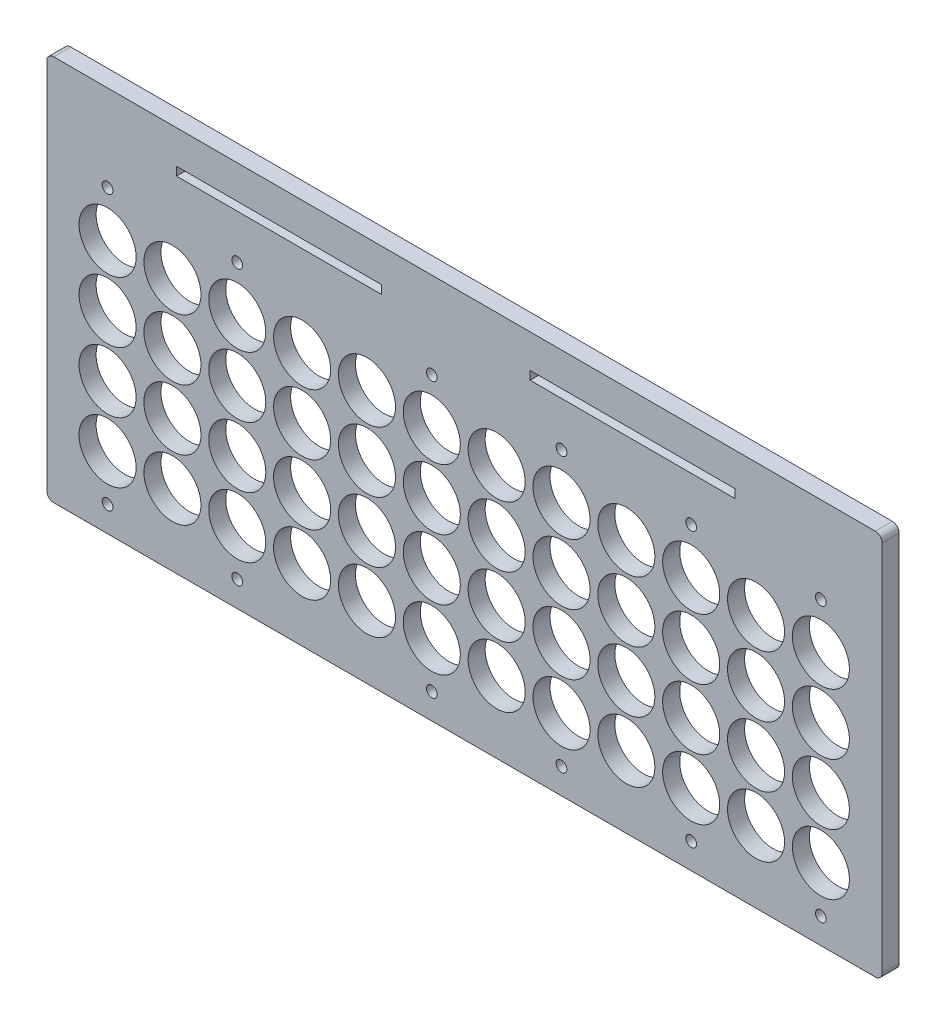
SolidWorks part; units mm, degrees
material "ABS"
ref_plane "X-Y Datum" through (0, 0, 0) normal (0, 0, 1) x (1, 0, 0)
ref_plane "X-Z Datum" through (0, 0, 0) normal (0, 1, 0) x (1, 0, 0)
ref_plane "Y-Z Datum" through (0, 0, 0) normal (1, 0, 0) x (0, 0, -1)
sketch "Sketch1" plane through (0, 0, 0) normal (0, 0, 1) x (1, 0, 0)
  line L1 (-10.2406, 8) -> (78.318, 8)
  line L2 (-10.2406, 8) -> (-10.2406, 16.1972)
  line L7 (-10.2406, 16.1972) -> (78.318, 16.1972)
  line L8 (78.318, 8) -> (78.318, 16.1972)
  line L12 (84.583, 16.1972) -> (87.883, 16.1972) construction
  line L17 (84.583, 4.7) -> (87.883, 4.7) construction
  line L20 (78.318, 0) -> (82.128, 0) construction
  circle A0 centre (0, 0) radius 10.5
  circle A24 centre (0, 0) radius 8 construction
  circle A25 centre (0, 0) radius 4.7 construction
  circle A46 centre (-3.5188, 13.3573) radius 2.5146 construction
  circle A47 centre (-3.5188, 13.3573) radius 1.1913 construction
  circle A78 centre (22.606, 0) radius 10.5
  circle A79 centre (22.606, 0) radius 8 construction
  circle A80 centre (22.606, 0) radius 4.7 construction
  circle A81 centre (45.212, 0) radius 10.5
  circle A82 centre (45.212, 0) radius 8 construction
  circle A83 centre (45.212, 0) radius 4.7 construction
  circle A84 centre (67.818, 0) radius 10.5
  circle A85 centre (67.818, 0) radius 8 construction
  circle A86 centre (67.818, 0) radius 4.7 construction
  circle A87 centre (0, 24.13) radius 10.5
  circle A88 centre (0, 24.13) radius 8 construction
  circle A89 centre (0, 24.13) radius 4.7 construction
  circle A90 centre (22.606, 24.13) radius 10.5
  circle A91 centre (22.606, 24.13) radius 8 construction
  circle A92 centre (22.606, 24.13) radius 4.7 construction
  circle A93 centre (45.212, 24.13) radius 10.5
  circle A94 centre (45.212, 24.13) radius 8 construction
  circle A95 centre (45.212, 24.13) radius 4.7 construction
  circle A96 centre (67.818, 24.13) radius 10.5
  circle A97 centre (67.818, 24.13) radius 8 construction
  circle A98 centre (67.818, 24.13) radius 4.7 construction
  circle A99 centre (0, 48.26) radius 10.5
  circle A100 centre (0, 48.26) radius 8 construction
  circle A101 centre (0, 48.26) radius 4.7 construction
  circle A102 centre (22.606, 48.26) radius 10.5
  circle A103 centre (22.606, 48.26) radius 8 construction
  circle A104 centre (22.606, 48.26) radius 4.7 construction
  circle A105 centre (45.212, 48.26) radius 10.5
  circle A106 centre (45.212, 48.26) radius 8 construction
  circle A107 centre (45.212, 48.26) radius 4.7 construction
  circle A108 centre (67.818, 48.26) radius 10.5
  circle A109 centre (67.818, 48.26) radius 8 construction
  circle A110 centre (67.818, 48.26) radius 4.7 construction
  circle A111 centre (0, 72.39) radius 10.5
  circle A112 centre (0, 72.39) radius 8 construction
  circle A113 centre (0, 72.39) radius 4.7 construction
  circle A114 centre (22.606, 72.39) radius 10.5
  circle A115 centre (22.606, 72.39) radius 8 construction
  circle A116 centre (22.606, 72.39) radius 4.7 construction
  circle A117 centre (45.212, 72.39) radius 10.5
  circle A118 centre (45.212, 72.39) radius 8 construction
  circle A119 centre (45.212, 72.39) radius 4.7 construction
  circle A120 centre (67.818, 72.39) radius 10.5
  circle A121 centre (67.818, 72.39) radius 8 construction
  circle A122 centre (67.818, 72.39) radius 4.7 construction
  circle A123 centre (0, 96.52) radius 10.5
  circle A124 centre (0, 96.52) radius 8 construction
  circle A125 centre (0, 96.52) radius 4.7 construction
  circle A126 centre (22.606, 96.52) radius 10.5
  circle A127 centre (22.606, 96.52) radius 8 construction
  circle A128 centre (22.606, 96.52) radius 4.7 construction
  circle A129 centre (45.212, 96.52) radius 10.5
  circle A130 centre (45.212, 96.52) radius 8 construction
  circle A131 centre (45.212, 96.52) radius 4.7 construction
  circle A132 centre (67.818, 96.52) radius 10.5
  circle A133 centre (67.818, 96.52) radius 8 construction
  circle A134 centre (67.818, 96.52) radius 4.7 construction
  circle A135 centre (0, 120.65) radius 10.5
  circle A136 centre (0, 120.65) radius 8 construction
  circle A137 centre (0, 120.65) radius 4.7 construction
  circle A138 centre (22.606, 120.65) radius 10.5
  circle A139 centre (22.606, 120.65) radius 8 construction
  circle A140 centre (22.606, 120.65) radius 4.7 construction
  circle A141 centre (45.212, 120.65) radius 10.5
  circle A142 centre (45.212, 120.65) radius 8 construction
  circle A143 centre (45.212, 120.65) radius 4.7 construction
  circle A144 centre (67.818, 120.65) radius 10.5
  circle A145 centre (67.818, 120.65) radius 8 construction
  circle A146 centre (67.818, 120.65) radius 4.7 construction
  dimension "D1" = 4
  dimension "D9" = 9.4
  dimension "D4" = 2.5
  dimension "D2" = 6
sketch "Sketch2" plane through (0, 0, 0) normal (0, 0, 1) x (1, 0, 0)
  line L0 (28.8471, 78.318) -> (28.8471, -10.5) construction
  line L5 (4.7, 78.318) -> (19.43, 78.318) construction
  line L6 (4.7, 78.318) -> (4.7, -10.5) construction
  line L7 (4.7, -10.5) -> (19.43, -10.5) construction
  line L8 (19.43, 78.318) -> (19.43, -10.5) construction
  line L9 (28.8471, 78.318) -> (43.5771, 78.318) construction
  line L10 (43.5771, 78.318) -> (43.5771, -10.5) construction
  line L11 (28.8471, -10.5) -> (43.5771, -10.5) construction
  line L12 (52.9942, 78.318) -> (52.9942, -10.5) construction
  line L13 (52.9942, 78.318) -> (67.7242, 78.318) construction
  line L14 (67.7242, 78.318) -> (67.7242, -10.5) construction
  line L15 (52.9942, -10.5) -> (67.7242, -10.5) construction
  line L16 (77.1413, 78.318) -> (77.1413, -10.5) construction
  line L17 (77.1413, 78.318) -> (91.8713, 78.318) construction
  line L18 (91.8713, 78.318) -> (91.8713, -10.5) construction
  line L19 (77.1413, -10.5) -> (91.8713, -10.5) construction
  line L20 (101.2884, 78.318) -> (101.2884, -10.5) construction
  line L21 (101.2884, 78.318) -> (116.0184, 78.318) construction
  line L22 (116.0184, 78.318) -> (116.0184, -10.5) construction
  line L23 (101.2884, -10.5) -> (116.0184, -10.5) construction
  line L24 (125.4355, 78.318) -> (125.4355, -10.5) construction
  line L25 (125.4355, 78.318) -> (140.1655, 78.318) construction
  line L26 (140.1655, 78.318) -> (140.1655, -10.5) construction
  line L27 (125.4355, -10.5) -> (140.1655, -10.5) construction
  line L28 (149.5826, 78.318) -> (149.5826, -10.5) construction
  line L29 (149.5826, 78.318) -> (164.3126, 78.318) construction
  line L30 (164.3126, 78.318) -> (164.3126, -10.5) construction
  line L31 (149.5826, -10.5) -> (164.3126, -10.5) construction
  line L32 (173.7297, 78.318) -> (173.7297, -10.5) construction
  line L33 (173.7297, 78.318) -> (188.4597, 78.318) construction
  line L34 (188.4597, 78.318) -> (188.4597, -10.5) construction
  line L35 (173.7297, -10.5) -> (188.4597, -10.5) construction
  line L36 (197.8768, 78.318) -> (197.8768, -10.5) construction
  line L37 (197.8768, 78.318) -> (212.6068, 78.318) construction
  line L38 (212.6068, 78.318) -> (212.6068, -10.5) construction
  line L39 (197.8768, -10.5) -> (212.6068, -10.5) construction
  line L40 (222.0239, 78.318) -> (222.0239, -10.5) construction
  line L41 (222.0239, 78.318) -> (236.7539, 78.318) construction
  line L42 (236.7539, 78.318) -> (236.7539, -10.5) construction
  line L43 (222.0239, -10.5) -> (236.7539, -10.5) construction
  line L44 (246.171, 78.318) -> (246.171, -10.5) construction
  line L45 (246.171, 78.318) -> (260.901, 78.318) construction
  line L46 (260.901, 78.318) -> (260.901, -10.5) construction
  line L47 (246.171, -10.5) -> (260.901, -10.5) construction
  line L48 (270.3181, 78.318) -> (270.3181, -10.5) construction
  line L49 (270.3181, 78.318) -> (285.0481, 78.318) construction
  line L50 (285.0481, 78.318) -> (285.0481, -10.5) construction
  line L51 (270.3181, -10.5) -> (285.0481, -10.5) construction
  line L52 (-19.43, 78.318) -> (-19.43, -10.5) construction
  line L53 (-19.43, 78.318) -> (-4.7, 78.318) construction
  line L54 (-4.7, 78.318) -> (-4.7, -10.5) construction
  line L55 (-19.43, -10.5) -> (-4.7, -10.5) construction
  line L56 (0, 78.4352) -> (0, 91.4087) construction
  line L57 (0, -10.6172) -> (0, -23.708) construction
  line L58 (-27.6439, 33.909) -> (301.0934, 33.909) construction
  line L59 (-19.43, 91.526) -> (285.0481, 91.526) construction
  line L60 (-19.43, 91.526) -> (-19.43, -23.708)
  line L61 (-19.43, -23.708) -> (285.0481, -23.708) construction
  line L62 (285.0481, 91.526) -> (285.0481, -23.708)
  line L63 (-19.43, 91.526) -> (-19.43, 94.447)
  line L64 (-19.43, 94.447) -> (285.0481, 94.447)
  line L65 (285.0481, 94.447) -> (285.0481, 91.526)
  line L66 (-19.43, -23.708) -> (-19.43, -26.629)
  line L67 (-19.43, -26.629) -> (285.0481, -26.629)
  line L68 (285.0481, -26.629) -> (285.0481, -23.708)
  circle A0 centre (0, 0) radius 10.6172
  circle A8 centre (0, 0) radius 4.7 construction
  circle A10 centre (24.13, 0) radius 10.6172
  circle A11 centre (48.26, 0) radius 10.6172
  circle A12 centre (72.39, 0) radius 10.6172
  circle A13 centre (24.13, 22.606) radius 10.6172
  circle A14 centre (48.26, 22.606) radius 10.6172
  circle A15 centre (72.39, 22.606) radius 10.6172
  circle A16 centre (24.13, 45.212) radius 10.6172
  circle A17 centre (48.26, 45.212) radius 10.6172
  circle A18 centre (72.39, 45.212) radius 10.6172
  circle A19 centre (24.13, 67.818) radius 10.6172
  circle A20 centre (48.26, 67.818) radius 10.6172
  circle A21 centre (72.39, 67.818) radius 10.6172
  circle A28 centre (0, 22.606) radius 10.6172
  circle A29 centre (0, 45.212) radius 10.6172
  circle A30 centre (0, 67.818) radius 10.6172
  circle A33 centre (0, 0) radius 8 construction
  circle A34 centre (96.52, 0) radius 10.6172
  circle A35 centre (120.65, 0) radius 10.6172
  circle A36 centre (144.78, 0) radius 10.6172
  circle A37 centre (168.91, 0) radius 10.6172
  circle A38 centre (193.04, 0) radius 10.6172
  circle A39 centre (217.17, 0) radius 10.6172
  circle A40 centre (241.3, 0) radius 10.6172
  circle A41 centre (265.43, 0) radius 10.6172
  circle A42 centre (96.52, 22.606) radius 10.6172
  circle A43 centre (120.65, 22.606) radius 10.6172
  circle A44 centre (144.78, 22.606) radius 10.6172
  circle A45 centre (168.91, 22.606) radius 10.6172
  circle A46 centre (193.04, 22.606) radius 10.6172
  circle A47 centre (217.17, 22.606) radius 10.6172
  circle A48 centre (241.3, 22.606) radius 10.6172
  circle A49 centre (265.43, 22.606) radius 10.6172
  circle A50 centre (96.52, 45.212) radius 10.6172
  circle A51 centre (120.65, 45.212) radius 10.6172
  circle A52 centre (144.78, 45.212) radius 10.6172
  circle A53 centre (168.91, 45.212) radius 10.6172
  circle A54 centre (193.04, 45.212) radius 10.6172
  circle A55 centre (217.17, 45.212) radius 10.6172
  circle A56 centre (241.3, 45.212) radius 10.6172
  circle A57 centre (265.43, 45.212) radius 10.6172
  circle A58 centre (96.52, 67.818) radius 10.6172
  circle A59 centre (120.65, 67.818) radius 10.6172
  circle A60 centre (144.78, 67.818) radius 10.6172
  circle A61 centre (168.91, 67.818) radius 10.6172
  circle A62 centre (193.04, 67.818) radius 10.6172
  circle A63 centre (217.17, 67.818) radius 10.6172
  circle A64 centre (241.3, 67.818) radius 10.6172
  circle A65 centre (265.43, 67.818) radius 10.6172
  circle A82 centre (24.13, 0) radius 8 construction
  circle A83 centre (24.13, 0) radius 4.7 construction
  circle A84 centre (48.26, 0) radius 8 construction
  circle A85 centre (48.26, 0) radius 4.7 construction
  circle A86 centre (72.39, 0) radius 8 construction
  circle A87 centre (72.39, 0) radius 4.7 construction
  circle A88 centre (96.52, 0) radius 8 construction
  circle A89 centre (96.52, 0) radius 4.7 construction
  circle A90 centre (120.65, 0) radius 8 construction
  circle A91 centre (120.65, 0) radius 4.7 construction
  circle A92 centre (144.78, 0) radius 8 construction
  circle A93 centre (144.78, 0) radius 4.7 construction
  circle A94 centre (168.91, 0) radius 8 construction
  circle A95 centre (168.91, 0) radius 4.7 construction
  circle A96 centre (193.04, 0) radius 8 construction
  circle A97 centre (193.04, 0) radius 4.7 construction
  circle A98 centre (217.17, 0) radius 8 construction
  circle A99 centre (217.17, 0) radius 4.7 construction
  circle A100 centre (241.3, 0) radius 8 construction
  circle A101 centre (241.3, 0) radius 4.7 construction
  circle A102 centre (265.43, 0) radius 8 construction
  circle A103 centre (265.43, 0) radius 4.7 construction
  circle A104 centre (24.13, 22.606) radius 8 construction
  circle A105 centre (24.13, 22.606) radius 4.7 construction
  circle A106 centre (48.26, 22.606) radius 8 construction
  circle A107 centre (48.26, 22.606) radius 4.7 construction
  circle A108 centre (72.39, 22.606) radius 8 construction
  circle A109 centre (72.39, 22.606) radius 4.7 construction
  circle A110 centre (96.52, 22.606) radius 8 construction
  circle A111 centre (96.52, 22.606) radius 4.7 construction
  circle A112 centre (120.65, 22.606) radius 8 construction
  circle A113 centre (120.65, 22.606) radius 4.7 construction
  circle A114 centre (144.78, 22.606) radius 8 construction
  circle A115 centre (144.78, 22.606) radius 4.7 construction
  circle A116 centre (168.91, 22.606) radius 8 construction
  circle A117 centre (168.91, 22.606) radius 4.7 construction
  circle A118 centre (193.04, 22.606) radius 8 construction
  circle A119 centre (193.04, 22.606) radius 4.7 construction
  circle A120 centre (217.17, 22.606) radius 8 construction
  circle A121 centre (217.17, 22.606) radius 4.7 construction
  circle A122 centre (241.3, 22.606) radius 8 construction
  circle A123 centre (241.3, 22.606) radius 4.7 construction
  circle A124 centre (265.43, 22.606) radius 8 construction
  circle A125 centre (265.43, 22.606) radius 4.7 construction
  circle A126 centre (24.13, 45.212) radius 8 construction
  circle A127 centre (24.13, 45.212) radius 4.7 construction
  circle A128 centre (48.26, 45.212) radius 8 construction
  circle A129 centre (48.26, 45.212) radius 4.7 construction
  circle A130 centre (72.39, 45.212) radius 8 construction
  circle A131 centre (72.39, 45.212) radius 4.7 construction
  circle A132 centre (96.52, 45.212) radius 8 construction
  circle A133 centre (96.52, 45.212) radius 4.7 construction
  circle A134 centre (120.65, 45.212) radius 8 construction
  circle A135 centre (120.65, 45.212) radius 4.7 construction
  circle A136 centre (144.78, 45.212) radius 8 construction
  circle A137 centre (144.78, 45.212) radius 4.7 construction
  circle A138 centre (168.91, 45.212) radius 8 construction
  circle A139 centre (168.91, 45.212) radius 4.7 construction
  circle A140 centre (193.04, 45.212) radius 8 construction
  circle A141 centre (193.04, 45.212) radius 4.7 construction
  circle A142 centre (217.17, 45.212) radius 8 construction
  circle A143 centre (217.17, 45.212) radius 4.7 construction
  circle A144 centre (241.3, 45.212) radius 8 construction
  circle A145 centre (241.3, 45.212) radius 4.7 construction
  circle A146 centre (265.43, 45.212) radius 8 construction
  circle A147 centre (265.43, 45.212) radius 4.7 construction
  circle A148 centre (24.13, 67.818) radius 8 construction
  circle A149 centre (24.13, 67.818) radius 4.7 construction
  circle A150 centre (48.26, 67.818) radius 8 construction
  circle A151 centre (48.26, 67.818) radius 4.7 construction
  circle A152 centre (72.39, 67.818) radius 8 construction
  circle A153 centre (72.39, 67.818) radius 4.7 construction
  circle A154 centre (96.52, 67.818) radius 8 construction
  circle A155 centre (96.52, 67.818) radius 4.7 construction
  circle A156 centre (120.65, 67.818) radius 8 construction
  circle A157 centre (120.65, 67.818) radius 4.7 construction
  circle A158 centre (144.78, 67.818) radius 8 construction
  circle A159 centre (144.78, 67.818) radius 4.7 construction
  circle A160 centre (168.91, 67.818) radius 8 construction
  circle A161 centre (168.91, 67.818) radius 4.7 construction
  circle A162 centre (193.04, 67.818) radius 8 construction
  circle A163 centre (193.04, 67.818) radius 4.7 construction
  circle A164 centre (217.17, 67.818) radius 8 construction
  circle A165 centre (217.17, 67.818) radius 4.7 construction
  circle A166 centre (241.3, 67.818) radius 8 construction
  circle A167 centre (241.3, 67.818) radius 4.7 construction
  circle A168 centre (265.43, 67.818) radius 8 construction
  circle A169 centre (265.43, 67.818) radius 4.7 construction
  circle A170 centre (0, 22.606) radius 8 construction
  circle A171 centre (0, 22.606) radius 4.7 construction
  circle A172 centre (0, 45.212) radius 8 construction
  circle A173 centre (0, 45.212) radius 4.7 construction
  circle A174 centre (0, 67.818) radius 8 construction
  circle A175 centre (0, 67.818) radius 4.7 construction
  circle A178 centre (0, 84.922) radius 2
  circle A181 centre (48.26, 84.922) radius 2
  circle A188 centre (217.17, 84.922) radius 2
  circle A190 centre (265.43, 84.922) radius 2
  circle A191 centre (24.13, 84.922) radius 2 [skipped]
  circle A192 centre (72.39, 84.922) radius 2 [skipped]
  circle A193 centre (120.65, 84.922) radius 2
  circle A194 centre (193.04, 84.922) radius 2 [skipped]
  circle A195 centre (241.3, 84.922) radius 2 [skipped]
  circle A196 centre (168.91, 84.922) radius 2
  circle A197 centre (265.43, -17.104) radius 2
  circle A198 centre (217.17, -17.104) radius 2
  circle A201 centre (48.26, -17.104) radius 2
  circle A202 centre (0, -17.104) radius 2
  circle A203 centre (96.52, 84.922) radius 2 [skipped]
  circle A204 centre (144.78, 84.922) radius 2 [skipped]
  circle A205 centre (168.91, -17.104) radius 2
  circle A206 centre (120.65, -17.104) radius 2
  dimension "D1" = 12
  dimension "D3" = 12
  dimension "D5" = 12
  dimension "D6" = 17.104
  dimension "D2" = 4
  dimension "D4" = 2
extrude "Boss-Extrude1" add sketch "Sketch2" along normal blind 6.35
sketch "Sketch3" plane through (0, 0, 6.35) normal (0, 0, 1) x (1, 0, 0)
  line L0 (10.6172, 67.818) -> (13.5128, 67.818) construction
  line L1 (4.7, 78.318) -> (19.43, 78.318) construction
  line L2 (4.7, 78.318) -> (4.7, -10.5) construction
  line L3 (4.7, -10.5) -> (19.43, -10.5) construction
  line L4 (19.43, 78.318) -> (19.43, -10.5) construction
  line L5 (12.065, 67.818) -> (12.065, 78.318) construction
  line L6 (4.7, 33.909) -> (19.43, 33.909) construction
  line L7 (10.6172, 0) -> (13.5128, 0) construction
  circle A0 centre (0, 0) radius 4.7 construction
  circle A1 centre (0, 0) radius 6.2 construction
  circle A2 centre (0, 67.818) radius 10.6172 construction
  circle A3 centre (24.13, 67.818) radius 10.6172 construction
  circle A4 centre (12.065, 77.8952) radius 4.1656 construction
  circle A5 centre (12.065, 77.8952) radius 3.81
  circle A6 centre (12.065, -10.0772) radius 3.81
  circle A7 centre (12.065, -10.0772) radius 4.1656 construction
  circle A32 centre (36.195, 77.8952) radius 3.81
  circle A33 centre (60.325, 77.8952) radius 3.81
  circle A34 centre (84.455, 77.8952) radius 3.81
  circle A35 centre (108.585, 77.8952) radius 3.81
  circle A36 centre (132.715, 77.8952) radius 3.81
  circle A37 centre (156.845, 77.8952) radius 3.81
  circle A38 centre (180.975, 77.8952) radius 3.81
  circle A39 centre (205.105, 77.8952) radius 3.81
  circle A40 centre (229.235, 77.8952) radius 3.81
  circle A41 centre (253.365, 77.8952) radius 3.81
  circle A42 centre (277.495, 77.8952) radius 3.81
  circle A43 centre (-12.065, 77.8952) radius 3.81
  circle A44 centre (277.495, -10.0772) radius 3.81
  circle A45 centre (253.365, -10.0772) radius 3.81
  circle A46 centre (229.235, -10.0772) radius 3.81
  circle A47 centre (205.105, -10.0772) radius 3.81
  circle A48 centre (180.975, -10.0772) radius 3.81
  circle A49 centre (156.845, -10.0772) radius 3.81
  circle A50 centre (132.715, -10.0772) radius 3.81
  circle A51 centre (108.585, -10.0772) radius 3.81
  circle A52 centre (84.455, -10.0772) radius 3.81
  circle A53 centre (60.325, -10.0772) radius 3.81
  circle A54 centre (36.195, -10.0772) radius 3.81
  circle A55 centre (-12.065, -10.0772) radius 3.81
  circle A56 centre (12.065, 33.909) radius 3.81
  circle A57 centre (36.195, 33.909) radius 3.81
  circle A58 centre (60.325, 33.909) radius 3.81
  circle A59 centre (84.455, 33.909) radius 3.81
  circle A60 centre (108.585, 33.909) radius 3.81
  circle A61 centre (132.715, 33.909) radius 3.81
  circle A62 centre (156.845, 33.909) radius 3.81
  circle A63 centre (180.975, 33.909) radius 3.81
  circle A64 centre (205.105, 33.909) radius 3.81
  circle A65 centre (229.235, 33.909) radius 3.81
  circle A66 centre (253.365, 33.909) radius 3.81
  circle A67 centre (277.495, 33.909) radius 3.81
  circle A68 centre (-12.065, 33.909) radius 3.81
  circle A69 centre (0, 0) radius 10.6172 construction
  circle A70 centre (24.13, 0) radius 10.6172 construction
  dimension "D2" = 12
  dimension "D4" = 7.62
  dimension "D5" = 10.0772
  dimension "D6" = 10.0772
  dimension "D1" = 1.5
  dimension "D3" = 2
extrude "Cut-Extrude1" [suppressed] cut sketch "Sketch3" against normal through all
sketch "Sketch5" plane through (0, 0, 6.35) normal (0, 0, 1) x (1, 0, 0)
  line L1 (-19.43, 94.447) -> (-22.605, 94.447)
  line L2 (-19.43, 94.447) -> (-19.43, -26.629)
  line L3 (-19.43, -26.629) -> (-22.605, -26.629)
  line L4 (-22.605, 94.447) -> (-22.605, -26.629)
  line L5 (285.0481, 94.447) -> (288.2231, 94.447)
  line L6 (285.0481, 94.447) -> (285.0481, -26.629)
  line L7 (285.0481, -26.629) -> (288.2231, -26.629)
  line L8 (288.2231, 94.447) -> (288.2231, -26.629)
extrude "Boss-Extrude2" add sketch "Sketch5" against normal through all
sketch "Sketch6" plane through (0, 0, 6.35) normal (0, 0, 1) x (1, 0, 0)
  line L0 (-10.6172, 67.818) -> (276.0472, 67.818) construction
  circle A0 centre (0, 67.818) radius 10.6172 construction
  circle A1 centre (265.43, 67.818) radius 10.6172 construction
sketch "Sketch7" [suppressed] plane through (0, 0, 6.35) normal (0, 0, 1) x (1, 0, 0)
  line L0 (-19.43, -26.629) -> (0.3535, -26.629) construction
  line L1 (-19.43, -26.629) -> (285.0481, -26.629) construction
  line L10 (-19.43, 33.909) -> (302.2531, 33.909) construction
  line L11 (-19.43, 94.447) -> (-19.43, -26.629) construction
  line L12 (246.76, 93.177) -> (18.67, 93.177)
  line L16 (284.86, 117.064) -> (-19.43, 117.064)
  line L18 (-19.43, 117.064) -> (-19.43, 109.444)
  line L19 (-19.43, 109.444) -> (18.67, 109.444)
  line L20 (18.67, 109.444) -> (18.67, 93.177)
  line L21 (284.86, 117.064) -> (284.86, 109.444)
  line L22 (284.86, 109.444) -> (246.76, 109.444)
  line L23 (246.76, 109.444) -> (246.76, 93.177)
  line L24 (285.0481, 94.447) -> (-19.43, 94.447) construction
  dimension "D1" = 22.617
extrude "Boss-Extrude3" [suppressed] add sketch "Sketch7" against normal through all
sketch "Sketch8" plane through (0, 0, 6.35) normal (0, 0, 1) x (1, 0, 0)
  line L1 (-22.605, 94.447) -> (288.2231, 94.447)
  line L2 (-22.605, 94.447) -> (-22.605, 117.064)
  line L3 (-22.605, 117.064) -> (288.2231, 117.064)
  line L4 (288.2231, 94.447) -> (288.2231, 117.064)
extrude "Boss-Extrude4" add sketch "Sketch8" against normal through all
fillet "Fillet1" [suppressed] radius 2.54
fillet "Fillet2" radius 2.54 4 edges at (288.2231, -26.629, 3.175) (288.2231, 117.064, 3.175) (-22.605, -26.629, 3.175) (-22.605, 117.064, 3.175)
sketch "Sketch9" [suppressed] plane through (0, 0, 6.35) normal (0, 0, 1) x (1, 0, 0)
  line L0 (10.6172, 67.818) -> (12.065, 67.818) construction
  line L1 (0, 57.2008) -> (0, 55.8292) construction
  line L2 (12.065, 67.818) -> (12.065, 56.515) construction
  line L3 (0, 56.515) -> (12.065, 56.515) construction
  line L5 (48.26, 34.5948) -> (48.26, 33.2232) construction
  line L6 (48.26, 33.909) -> (36.195, 33.909) construction
  line L7 (36.195, 45.212) -> (36.195, 33.909) construction
  line L8 (12.065, 56.515) -> (36.195, 56.515)
  line L9 (12.065, 56.515) -> (12.065, 33.909)
  line L10 (12.065, 33.909) -> (36.195, 33.909)
  line L11 (36.195, 56.515) -> (36.195, 33.909)
  circle A0 centre (0, 67.818) radius 10.6172 construction
  circle A2 centre (0, 45.212) radius 10.6172 construction
  circle A4 centre (48.26, 45.212) radius 10.6172 construction
  circle A5 centre (48.26, 22.606) radius 10.6172 construction
sketch "Sketch10" [suppressed] plane through (0, 0, 6.35) normal (0, 0, 1) x (1, 0, 0)
  line L0 (132.715, 117.064) -> (132.715, 106.9616) construction
  line L1 (282.32, 117.064) -> (-16.89, 117.064) construction
  line L3 (153.035, 106.9616) -> (153.035, 99.3916)
  line L5 (112.395, 99.3916) -> (112.395, 106.9616)
  line L7 (236.5978, 104.6485) -> (160.3978, 104.6485)
  line L8 (28.8322, 101.4735) -> (105.0322, 101.4735)
  line L9 (28.8322, 101.4735) -> (28.8322, 104.6485)
  line L10 (28.8322, 104.6485) -> (105.0322, 104.6485)
  line L11 (105.0322, 101.4735) -> (105.0322, 104.6485)
  line L12 (28.8322, 101.4735) -> (105.0322, 104.6485) construction
  line L13 (28.8322, 104.6485) -> (105.0322, 101.4735) construction
  line L14 (160.3978, 101.4735) -> (160.3978, 104.6485)
  line L15 (236.5978, 101.4735) -> (160.3978, 101.4735)
  line L16 (236.5978, 101.4735) -> (236.5978, 104.6485)
  line L17 (112.395, 106.9616) -> (112.395, 107.5966)
  line L18 (-16.89, 117.064) -> (23.695, 117.064) construction
  line L19 (-16.89, 117.064) -> (-16.89, 92.1703) construction
  line L20 (-16.89, 92.1703) -> (23.695, 92.1703) construction
  line L21 (23.695, 117.064) -> (23.695, 92.1703) construction
  line L22 (112.395, 107.5966) -> (153.035, 107.5966)
  line L23 (153.035, 107.5966) -> (153.035, 106.9616)
  line L24 (112.395, 99.3916) -> (112.395, 98.7566)
  line L25 (112.395, 98.7566) -> (153.035, 98.7566)
  line L26 (153.035, 98.7566) -> (153.035, 99.3916)
  arc A0 (-16.89, 117.064) -> (-19.43, 114.524) centre (-16.89, 114.524) ccw construction
  point P8 (66.9322, 103.061)
extrude "Cut-Extrude2" [suppressed] cut sketch "Sketch10" against normal through all
fillet "Fillet3" [suppressed] radius 1.27
fillet "Fillet4" [suppressed] radius 1
sketch "Sketch11" plane through (0, 0, 6.35) normal (0, 0, 1) x (1, 0, 0)
  line L0 (129.54, 117.064) -> (129.54, 106.9616) construction
  line L1 (129.54, 106.9616) -> (149.86, 106.9616) construction
  line L2 (149.86, 106.9616) -> (149.86, 99.3916) construction
  line L3 (149.86, 99.3916) -> (109.22, 99.3916) construction
  line L4 (109.22, 99.3916) -> (109.22, 106.9616) construction
  line L5 (109.22, 106.9616) -> (129.54, 106.9616) construction
  line L6 (233.4228, 104.6485) -> (157.2228, 104.6485)
  line L7 (25.6572, 101.4735) -> (101.8572, 101.4735)
  line L8 (25.6572, 101.4735) -> (25.6572, 104.6485)
  line L9 (25.6572, 104.6485) -> (101.8572, 104.6485)
  line L10 (101.8572, 101.4735) -> (101.8572, 104.6485)
  line L11 (25.6572, 101.4735) -> (101.8572, 104.6485) construction
  line L12 (25.6572, 104.6485) -> (101.8572, 101.4735) construction
  line L13 (157.2228, 101.4735) -> (157.2228, 104.6485)
  line L14 (233.4228, 101.4735) -> (157.2228, 101.4735)
  line L15 (233.4228, 101.4735) -> (233.4228, 104.6485)
  line L16 (-20.065, 117.064) -> (20.52, 117.064) construction
  line L17 (-20.065, 117.064) -> (-20.065, 92.1703) construction
  line L18 (-20.065, 92.1703) -> (20.52, 92.1703) construction
  line L19 (20.52, 117.064) -> (20.52, 92.1703) construction
  point P6 (63.7572, 103.061)
  point P19 (-20.065, 117.064)
extrude "Cut-Extrude3" cut sketch "Sketch11" against normal through all both
